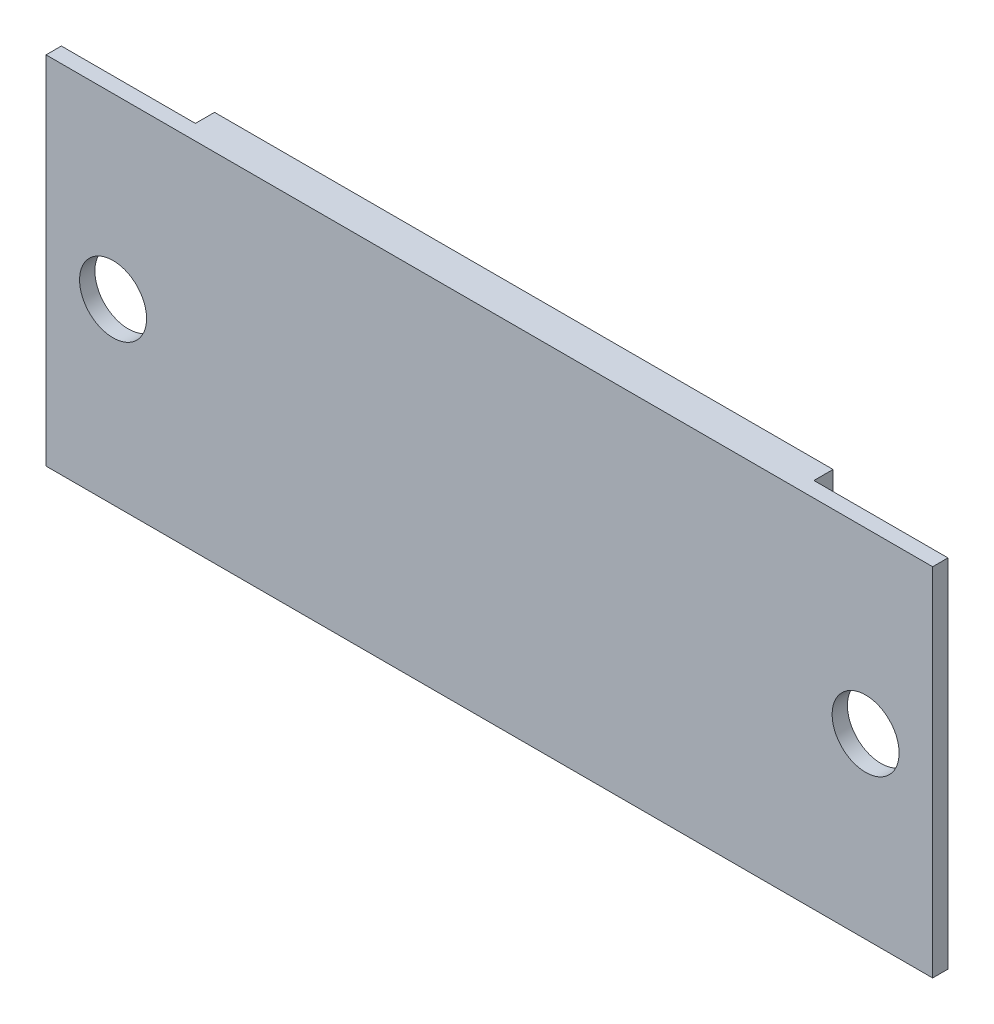
SolidWorks part; units mm, degrees
material "Glass"
ref_plane "Спереди" through (0, 0, 0) normal (0, 0, 1) x (1, 0, 0)
ref_plane "Сверху" through (0, 0, 0) normal (0, 1, 0) x (1, 0, 0)
ref_plane "Справа" through (0, 0, 0) normal (1, 0, 0) x (0, 0, -1)
sketch "Sketch1" plane through (0, 0, 0) normal (0, 0, 1) x (1, 0, 0)
  line L1 (-16.15, -9.3) -> (16.15, -9.3)
  line L2 (-16.15, -9.3) -> (-16.15, 9.3)
  line L3 (-16.15, 9.3) -> (16.15, 9.3)
  line L4 (16.15, -9.3) -> (16.15, 9.3)
  line L5 (-16.15, -9.3) -> (16.15, 9.3) construction
  line L6 (-16.15, 9.3) -> (16.15, -9.3) construction
  point P0 (0, 0)
  dimension "D1" = 32.3
  dimension "D2" = 18.6
extrude "Boss-Extrude1" add sketch "Sketch1" along normal blind 1.8
sketch "Sketch4" plane through (0, 0, 0) normal (0, 0, -1) x (-1, 0, 0)
  line L17 (-14.8, -7.95) -> (14.8, -7.95)
  line L18 (14.8, -7.95) -> (14.8, 7.95)
  line L19 (14.8, 7.95) -> (-14.8, 7.95)
  line L20 (-14.8, 7.95) -> (-14.8, -7.95)
  line L21 (-14.8, -7.95) -> (14.8, -7.95)
  line L22 (14.8, -7.95) -> (14.8, 7.95)
  line L23 (14.8, 7.95) -> (-14.8, 7.95)
  line L24 (-14.8, 7.95) -> (-14.8, -7.95)
  dimension "D1" = 1.35
extrude "Cut-Extrude2" [suppressed] cut sketch "Sketch4" against normal offset from surface (1.3 mm away) 0.5
sketch "Sketch5" plane through (0, 0, 1.8) normal (0, 0, 1) x (1, 0, 0)
  line L0 (0, 9.3) -> (0, -9.3) construction
  line L1 (16.15, 9.3) -> (-16.15, 9.3) construction
  line L2 (-16.15, -9.3) -> (16.15, -9.3) construction
  line L3 (-16.15, 9.3) -> (-16.15, -9.3) construction
  line L4 (-16.15, 9.3) -> (-16.15, -9.3)
  line L5 (-16.15, 9.3) -> (-23.15, 9.3)
  line L6 (-23.15, 9.3) -> (-23.15, -9.3)
  line L7 (-23.15, -9.3) -> (-16.15, -9.3)
  line L8 (23.15, -9.3) -> (16.15, -9.3)
  line L9 (23.15, 9.3) -> (23.15, -9.3)
  line L10 (16.15, 9.3) -> (16.15, -9.3)
  line L11 (16.15, 9.3) -> (23.15, 9.3)
  dimension "D1" = 7
extrude "Boss-Extrude3" add sketch "Sketch5" against normal offset from surface (0.8 mm away) 1 up to face at (0, 0, 0)
sketch "Sketch6" plane through (0, 0, 1.8) normal (0, 0, 1) x (1, 0, 0)
  line L0 (0, 9.3) -> (0, -9.3) construction
  line L1 (23.15, 9.3) -> (-23.15, 9.3) construction
  line L2 (-23.15, -9.3) -> (23.15, -9.3) construction
  line L3 (-19.65, 9.3) -> (-19.65, -9.3) construction
  line L4 (-23.15, 9.3) -> (-23.15, -9.3) construction
  circle A0 centre (-19.65, 0) radius 1.75
  circle A1 centre (19.65, 0) radius 1.75
  dimension "D2" = 3.5
  dimension "D1" = 19.65
  dimension "D3" = 3.5
extrude "Cut-Extrude3" cut sketch "Sketch6" against normal up to surface (0.8 mm away) up to face at (19.65, 0, 1)
